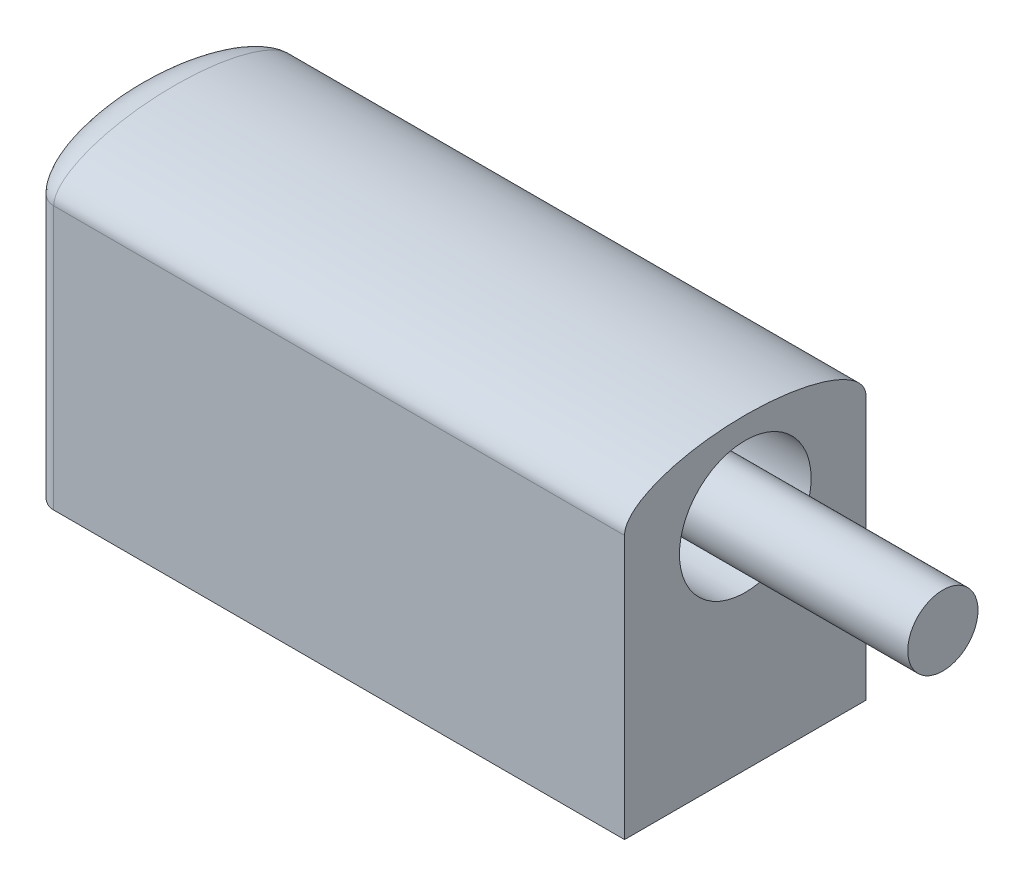
SolidWorks part; units mm, degrees
ref_plane "Alzado" through (0, 0, 0) normal (0, 0, 1) x (1, 0, 0)
ref_plane "Planta" through (0, 0, 0) normal (0, 1, 0) x (1, 0, 0)
ref_plane "Vista lateral" through (0, 0, 0) normal (1, 0, 0) x (0, 0, -1)
sketch "Croquis1" plane through (0, 0, 0) normal (0, 0, 1) x (1, 0, 0)
  line L0 (-14.4849, 9.6395) -> (11.5151, 9.6395)
  line L1 (-14.4849, 9.6395) -> (-14.4849, -2.3605)
  line L2 (-14.4849, -2.3605) -> (11.5151, -2.3605)
  line L3 (11.5151, -2.3605) -> (11.5151, 9.6395)
  dimension "D1" = 26
  dimension "D2" = 12
extrude "Saliente-Extruir1" add sketch "Croquis1" along normal blind 11
sketch "Croquis5" plane through (11.5151, 0, 0) normal (1, 0, 0) x (0, 0, -1)
  line L0 (-11, 9.6395) -> (0, 9.6395) construction
  ellipse E0 centre (-5.5, 9.6395) end of major axis (0, 9.6395) minor radius 2
  dimension "D1" = 2
extrude "Saliente-Extruir2" add sketch "Croquis5" against normal blind 26
sketch "Croquis6" plane through (0, -2.3605, 0) normal (0, -1, 0) x (1, 0, 0)
  line L0 (-14.4849, 11) -> (-14.4849, 0) construction
  ellipse E0 centre (-14.4849, 5.5) end of major axis (-14.4849, 0) minor radius 2
  dimension "D1" = 2
extrude "Saliente-Extruir3" add sketch "Croquis6" against normal blind 12
sketch "Croquis7" plane through (0, 9.6395, 0) normal (0, 1, 0) x (1, 0, 0)
sketch "Croquis8" plane through (-14.4849, 0, 0) normal (-1, 0, 0) x (0, 0, 1)
  line L0 (0, 9.6395) -> (11, 9.6395)
  line L1 (11, 9.6395) -> (0, 9.6395) construction
  ellipse E0 centre (5.5, 9.6395) end of major axis (0, 9.6395) minor radius 2 (11, 9.6395) -> (0, 9.6395) ccw
  ellipse E1 centre (5.5, 9.6395) end of major axis (0, 9.6395) minor radius 2 (11, 9.6395) -> (0, 9.6395) ccw construction
  point P6 (10.9741, 9.8229)
  point P7 (5.5, 11.6395)
revolve "Revolución2" add sketch "Croquis8" angle 90 about L0
sketch "Croquis9" plane through (11.5151, 0, 0) normal (1, 0, 0) x (0, 0, -1)
  line L0 (-5.5, 7.6395) -> (-5.5, 11.6395) construction
  line L2 (-5.5, 11.6395) -> (-10.4094, 11.6395) construction
  circle A0 centre (-5.5, 7.6395) radius 3
  ellipse E0 centre (-5.5, 9.6395) end of major axis (0, 9.6395) minor radius 2 (0, 9.6395) -> (-11, 9.6395) ccw construction
  dimension "D2" = 6
  dimension "D1" = 4
extrude "Cortar-Extruir1" cut sketch "Croquis9" against normal blind 5
sketch "Croquis11" plane through (6.5151, 0, 0) normal (1, 0, 0) x (0, 0, -1)
  circle A0 centre (-5.5, 7.6395) radius 1.6
  dimension "D1" = 3.2
extrude "Saliente-Extruir4" add sketch "Croquis11" along normal blind 14
sketch "Croquis12" plane through (0, -2.3605, 0) normal (0, -1, 0) x (1, 0, 0)
  line L0 (1.5151, 5.5) -> (11.5151, 5.5) construction
  line L1 (11.5151, 11) -> (11.5151, 0) construction
  circle A0 centre (1.5151, 5.5) radius 2.1
  circle A1 centre (-6.4849, 5.5) radius 2.1
  point P7 (0, 0)
  point P8 (0, 0)
  dimension "D2" = 4.2
  dimension "D3" = 4.2
  dimension "D1" = 10
  dimension "D4" = 8
extrude "Cortar-Extruir2" cut sketch "Croquis12" against normal blind 6
